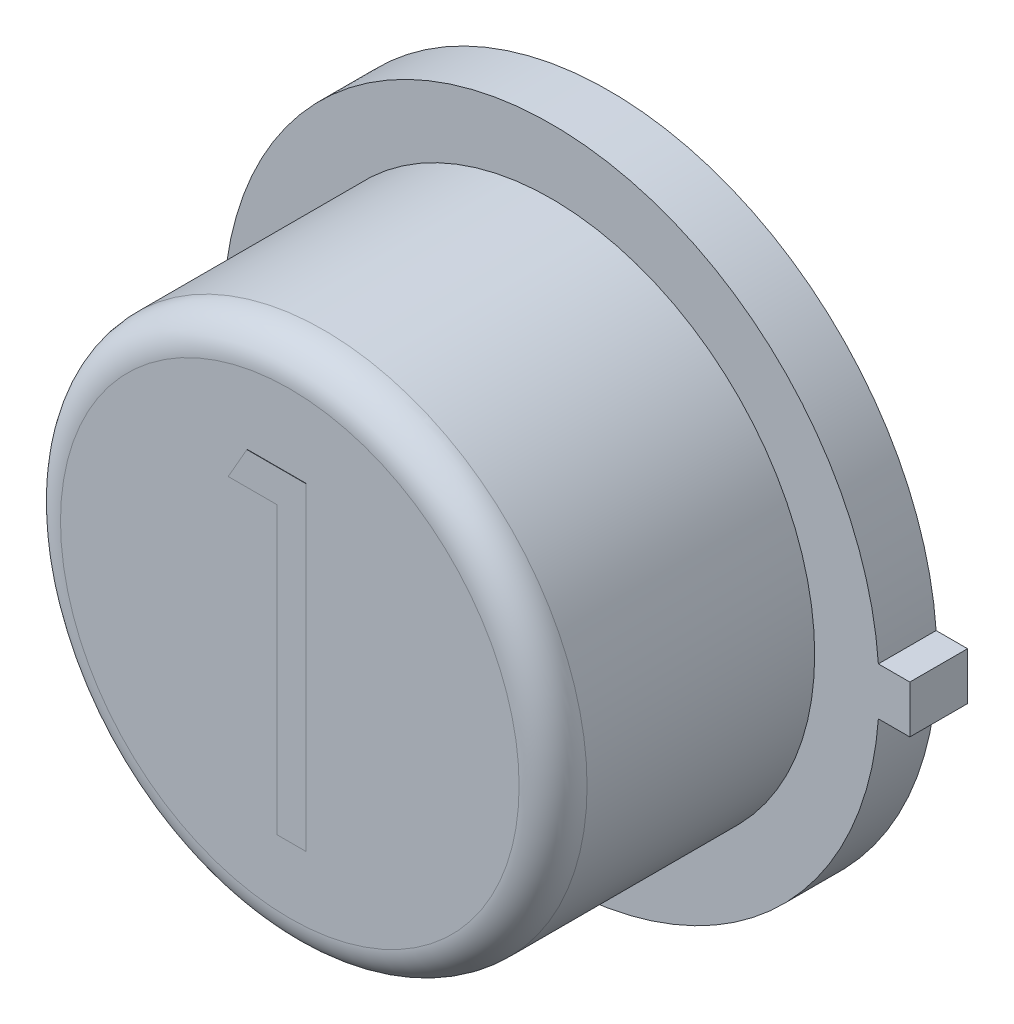
SolidWorks part; units mm, degrees
ref_plane "Front Plane" through (0, 0, 0) normal (0, 0, 1) x (1, 0, 0)
ref_plane "Top Plane" through (0, 0, 0) normal (0, 1, 0) x (1, 0, 0)
ref_plane "Right Plane" through (0, 0, 0) normal (1, 0, 0) x (0, 0, -1)
sketch "Sketch1" plane through (0, 0, 0) normal (0, 0, 1) x (1, 0, 0)
  line L1 (2.4511, 0.1778) -> (2.6797, 0.1778)
  line L3 (2.4511, -0.1778) -> (2.6797, -0.1778)
  line L4 (2.6797, 0.1778) -> (2.6797, -0.1778)
  line L5 (2.4511, 0.1778) -> (2.4444, 0.1778)
  line L6 (2.4511, -0.1778) -> (2.4446, -0.1778)
  arc A0 (2.4446, 0.1778) -> (2.4446, -0.1778) centre (0, 0) ccw
  dimension "D1" = 4.9022
  dimension "D2" = 0.3556
  dimension "D3" = 0.2286
extrude "Boss-Extrude1" add sketch "Sketch1" along normal blind 0.4318
sketch "Sketch2" plane through (0, 0, 0.4318) normal (0, 0, 1) x (1, 0, 0)
  circle A0 centre (0, 0) radius 1.9685
  dimension "D1" = 3.937
extrude "Boss-Extrude2" add sketch "Sketch2" along normal blind 1.9558
sketch "Sketch3" plane through (0, 0, 0) normal (0, 0, -1) x (-1, 0, 0)
  circle A0 centre (0, 0) radius 1.7576
extrude "Boss-Extrude3" add sketch "Sketch3" along normal blind 0.0025
fillet "Fillet1" radius 0.254 1 edges at (1.9685, 0, 2.3876)
sketch "Sketch4" plane through (0, 0, 2.3876) normal (0, 0, 1) x (1, 0, 0)
  line L0 (-1.2065, -1.2181) -> (1.2065, -1.2181) construction
  circle A0 centre (0, 0) radius 1.7145 construction
  text T0 "1" font "Century Gothic" height in points 9
  dimension "D1" = 2.413
extrude "Boss-Extrude4" add sketch "Sketch4" along normal blind 0.0025
